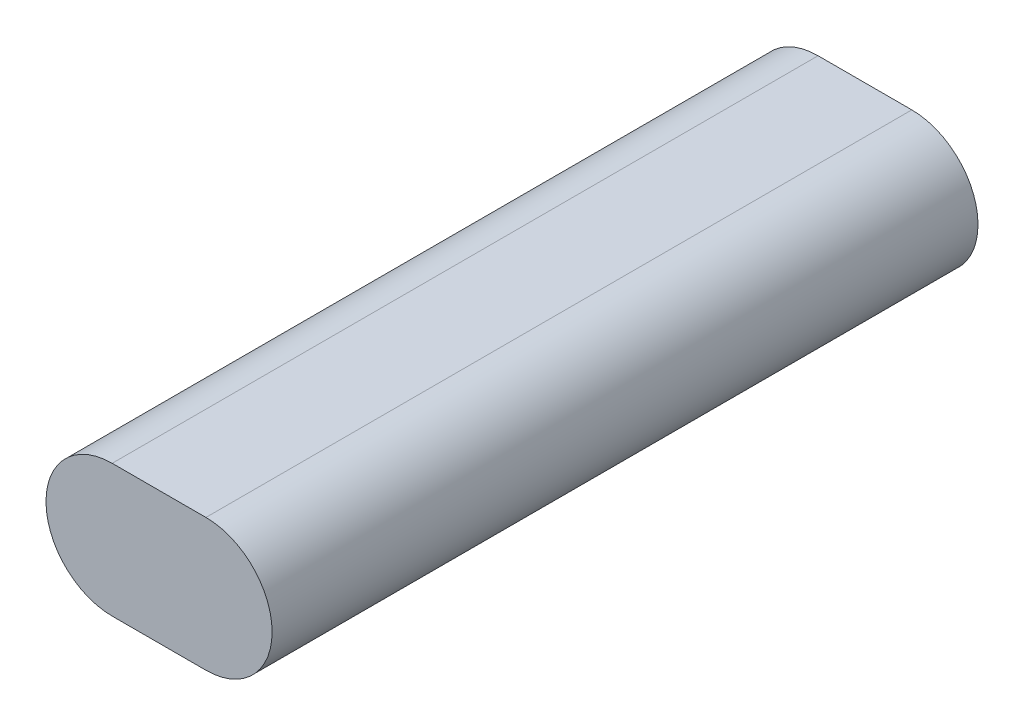
SolidWorks part; units mm, degrees
ref_plane "Ebene vorne" through (0, 0, 0) normal (0, 0, 1) x (1, 0, 0)
ref_plane "Ebene oben" through (0, 0, 0) normal (0, 1, 0) x (1, 0, 0)
ref_plane "Ebene rechts" through (0, 0, 0) normal (1, 0, 0) x (0, 0, -1)
sketch "Skizze1" plane through (0, 0, 0) normal (0, 0, 1) x (1, 0, 0)
  line L0 (-8.5, 0) -> (8.5, 0) construction
  line L1 (-8.5, 12) -> (8.5, 12)
  line L2 (-8.5, -12) -> (8.5, -12)
  arc A0 (-8.5, 12) -> (-8.5, -12) centre (-8.5, 0) ccw
  arc A1 (8.5, -12) -> (8.5, 12) centre (8.5, 0) ccw
  point P2 (0, 0)
  point P8 (-20.5, 0)
  point P9 (20.5, 0)
  dimension "D1" = 41
  dimension "D2" = 24
extrude "Aufsatz-Linear austragen1" add sketch "Skizze1" along normal blind 128
